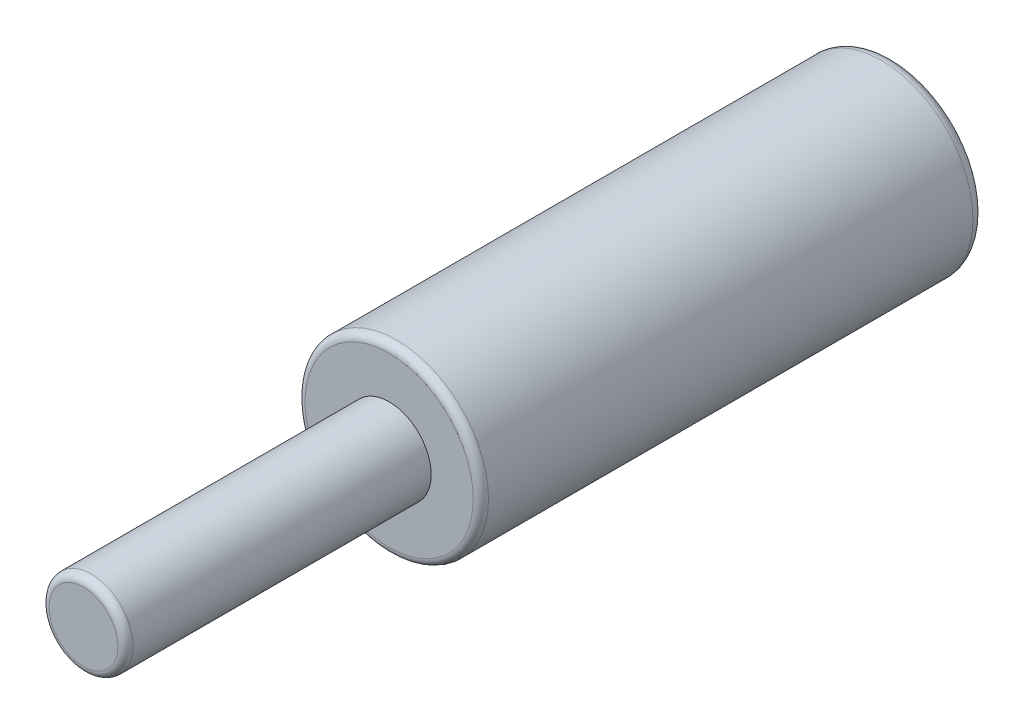
SolidWorks part; units mm, degrees
material "3.0517 (EN-AW 3003)"
ref_plane "Alzado" through (0, 0, 0) normal (0, 0, 1) x (1, 0, 0)
ref_plane "Planta" through (0, 0, 0) normal (0, 1, 0) x (1, 0, 0)
ref_plane "Vista lateral" through (0, 0, 0) normal (1, 0, 0) x (0, 0, -1)
sketch "Croquis1" plane through (0, 0, 0) normal (0, 0, 1) x (1, 0, 0)
  circle A0 centre (0, 0) radius 6
  circle A1 centre (0, 0) radius 3.5
extrude "Saliente-Extruir1" add sketch "Croquis1" along normal blind 28
sketch "Croquis2" plane through (0, 0, 28) normal (0, 0, 1) x (1, 0, 0)
  circle A0 centre (0, 0) radius 6
extrude "Saliente-Extruir2" add sketch "Croquis2" along normal blind 5
sketch "Croquis3" plane through (0, 0, 33) normal (0, 0, 1) x (1, 0, 0)
  circle A0 centre (0, 0) radius 2.75
extrude "Saliente-Extruir3" add sketch "Croquis3" along normal blind 20
fillet "Redondeo1" radius 0.5 1 edges at (6, 0, 33)
fillet "Redondeo2" radius 0.8 1 edges at (6, 0, 0)
fillet "Redondeo3" radius 0.5 1 edges at (2.75, 0, 53)
